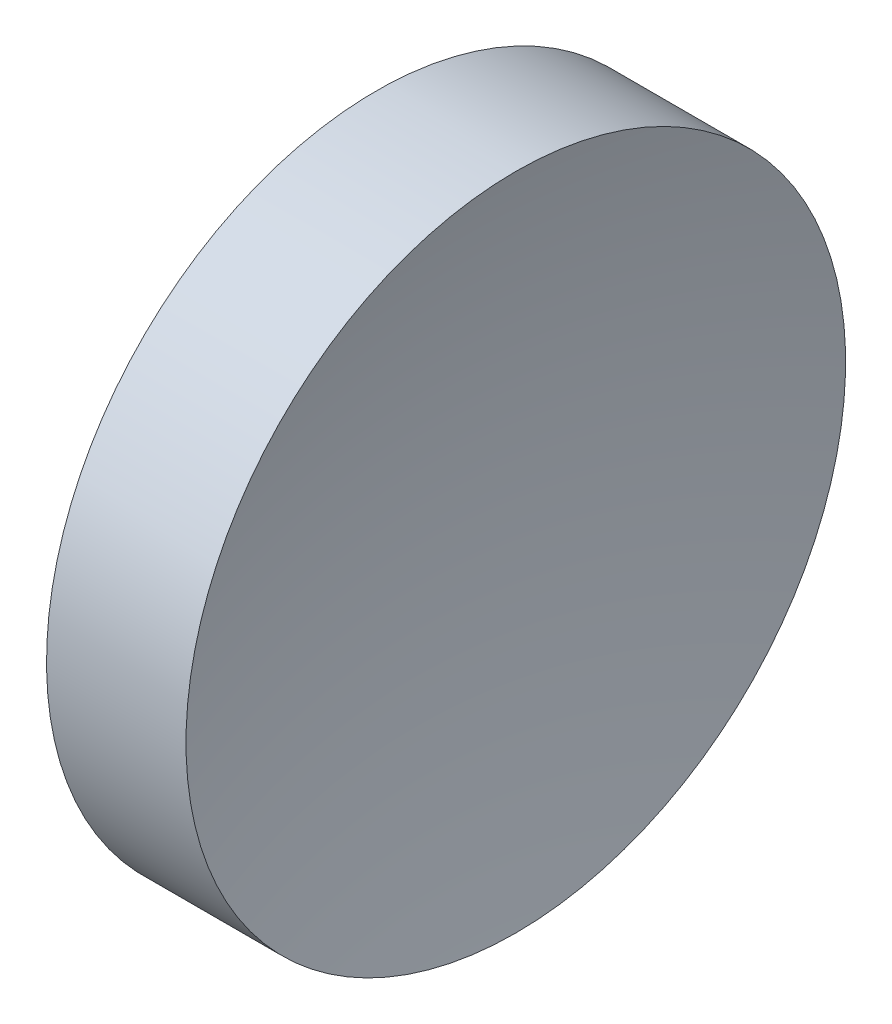
SolidWorks part; units mm, degrees
ref_plane "前视基准面" through (0, 0, 0) normal (0, 0, 1) x (1, 0, 0)
ref_plane "上视基准面" through (0, 0, 0) normal (0, 1, 0) x (1, 0, 0)
ref_plane "右视基准面" through (0, 0, 0) normal (1, 0, 0) x (0, 0, -1)
sketch "草图1" plane through (0, 0, 0) normal (0, 0, 1) x (1, 0, 0)
  line L0 (21.506, 13.0311) -> (26.997, 13.0311) construction
  line L1 (22.4242, 13.0311) -> (22.4242, 18.0311)
  line L2 (22.4242, 18.0311) -> (24.5387, 18.0311)
  line L3 (23.9242, 13.0311) -> (22.4242, 13.0311)
  arc A0 (24.5387, 18.0311) -> (23.9242, 13.0311) centre (44.5742, 13.0311) ccw
revolve "旋转1" add sketch "草图1" angle 360 about L0
